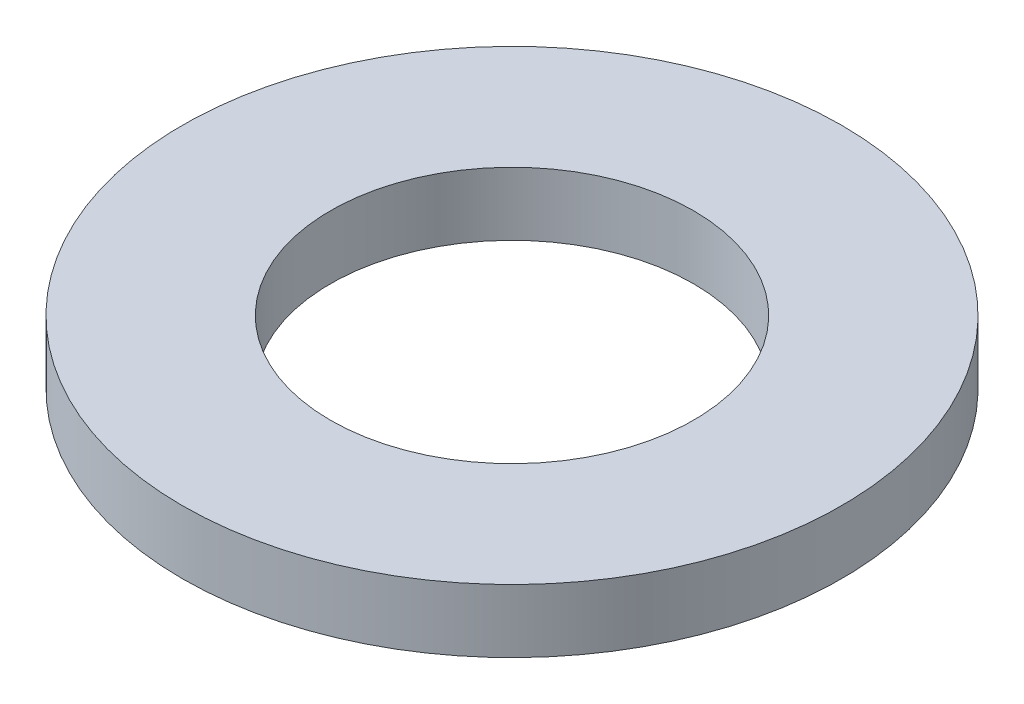
SolidWorks part; units mm, degrees
ref_plane "Front Plane" through (0, 0, 0) normal (0, 0, 1) x (1, 0, 0)
ref_plane "Top Plane" through (0, 0, 0) normal (0, 1, 0) x (1, 0, 0)
ref_plane "Right Plane" through (0, 0, 0) normal (1, 0, 0) x (0, 0, -1)
sketch "Sketch1" plane through (0, 0, 0) normal (0, 1, 0) x (1, 0, 0)
  circle A0 centre (0, 0) radius 4.4958
  dimension "OD" = 8.9916
extrude "Boss-Extrude1" add sketch "Sketch1" along normal blind 0.8636
sketch "Sketch5" plane through (0, 0.8636, 0) normal (0, 1, 0) x (-1, 0, 0)
  circle A0 centre (0, 0) radius 2.4765
  dimension "ID" = 4.953
extrude "Cut-Extrude1" cut sketch "Sketch5" against normal through all
